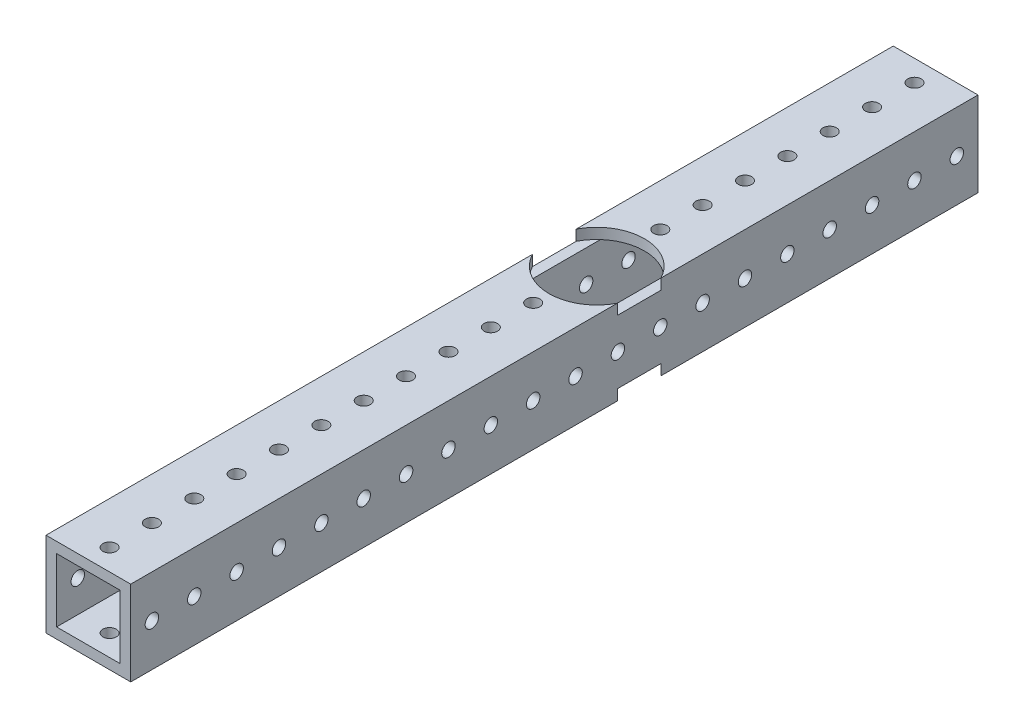
SolidWorks part; units mm, degrees
material "3003 Alloy"
ref_plane "Front Plane" through (0, 0, 0) normal (0, 0, 1) x (1, 0, 0)
ref_plane "Top Plane" through (0, 0, 0) normal (0, 1, 0) x (1, 0, 0)
ref_plane "Right Plane" through (0, 0, 0) normal (1, 0, 0) x (0, 0, -1)
sketch "Sketch1" plane through (0, 0, 0) normal (0, 0, 1) x (1, 0, 0)
  line L1 (-12.7, -12.7) -> (12.7, -12.7)
  line L2 (-12.7, -12.7) -> (-12.7, 12.7)
  line L3 (-12.7, 12.7) -> (12.7, 12.7)
  line L4 (12.7, -12.7) -> (12.7, 12.7)
  line L5 (-12.7, -12.7) -> (12.7, 12.7) construction
  line L6 (-12.7, 12.7) -> (12.7, -12.7) construction
  line L7 (-9.525, -9.525) -> (9.525, -9.525)
  line L8 (-9.525, -9.525) -> (-9.525, 9.525)
  line L9 (-9.525, 9.525) -> (9.525, 9.525)
  line L10 (9.525, -9.525) -> (9.525, 9.525)
  line L11 (-9.525, -9.525) -> (9.525, 9.525) construction
  line L12 (-9.525, 9.525) -> (9.525, -9.525) construction
  point P0 (0, 0)
  point P6 (0, 0)
  dimension "D1" = 25.4
  dimension "D2" = 19.05
extrude "Boss-Extrude1" add sketch "Sketch1" along normal mid plane 254
sketch "Sketch3" plane through (0, 12.7, 0) normal (0, 1, 0) x (1, 0, 0)
  line L0 (-12.7, -127) -> (-12.7, 127) construction
  line L1 (12.7, -127) -> (-12.7, -127) construction
  circle A2 centre (0, -120.65) radius 2.0193
  dimension "D1" = 4.0386
  dimension "D2" = 12.7
  dimension "D3" = 6.35
extrude "Cut-Extrude1" cut sketch "Sketch3" against normal through all contours A2
pattern_linear "LPattern1" count 20 spacing 12.7 along (0, 0, -1) of "Cut-Extrude1"
sketch "Sketch4" plane through (-12.7, 0, 0) normal (-1, 0, 0) x (0, 0, 1)
  line L0 (127, 12.7) -> (127, -12.7) construction
  line L1 (127, -12.7) -> (-127, -12.7) construction
  circle A0 centre (120.65, 0) radius 2.0193
  dimension "D1" = 4.0386
  dimension "D2" = 6.35
  dimension "D3" = 12.7
extrude "Cut-Extrude2" cut sketch "Sketch4" against normal through all
pattern_linear "LPattern2" count 20 spacing 12.7 along (0, 0, -1) of "Cut-Extrude2"
sketch "Sketch7" [suppressed] plane through (12.7, 0, 0) normal (1, 0, 0) x (0, 0, -1)
  circle A0 centre (-101.6, 0) radius 14.2875
  dimension "D1" = 28.575
  dimension "D2" = 101.6
extrude "Cut-Extrude5" [suppressed] cut sketch "Sketch7" against normal blind 3.175
mirror "Mirror3" [suppressed] about plane through (0, 0, 0) normal (1, 0, 0)
sketch "Sketch8" plane through (0, 12.7, 0) normal (0, 1, 0) x (1, 0, 0)
  line L0 (0, -13.97) -> (0, 13.97) construction
  line L1 (0, 69.85) -> (0, 57.15) construction
  circle A0 centre (0, 25.4) radius 14.2875
  point P0 (0, 37.0236)
  point P1 (0, 63.5)
  dimension "D1" = 28.575
  dimension "D2" = 38.1
extrude "Cut-Extrude6" cut sketch "Sketch8" against normal blind 3.175
mirror "Mirror4" about plane through (0, 0, 0) normal (0, 1, 0) of "Cut-Extrude6"
